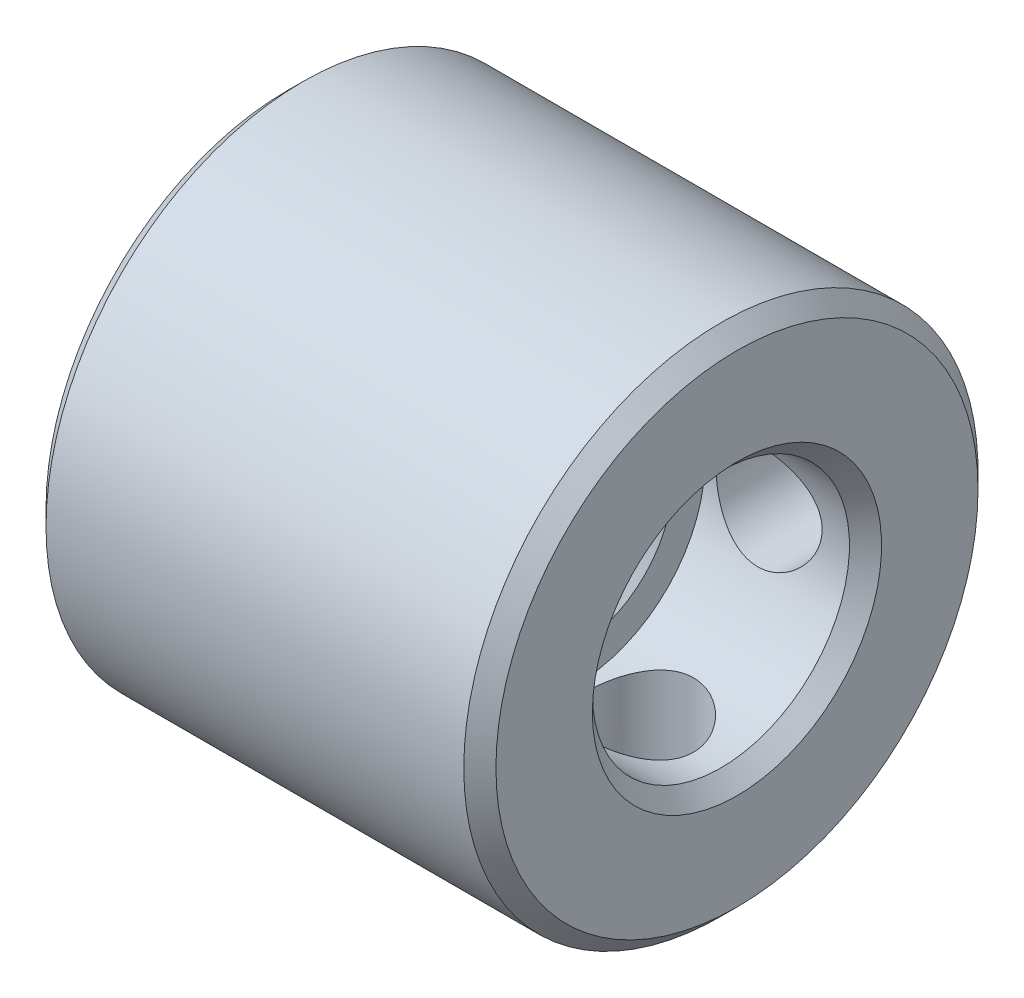
SolidWorks part; units mm, degrees
ref_plane "前视基准面" through (0, 0, 0) normal (0, 0, 1) x (1, 0, 0)
ref_plane "上视基准面" through (0, 0, 0) normal (0, 1, 0) x (1, 0, 0)
ref_plane "右视基准面" through (0, 0, 0) normal (1, 0, 0) x (0, 0, -1)
sketch "草图1" plane through (0, 0, 0) normal (0, 1, 0) x (1, 0, 0)
  line L0 (-5, 0) -> (10.2778, 0)
  line L1 (0, 8.5494) -> (0, -6.358)
  line L2 (0, 2.5) -> (9, 2.5)
  line L3 (9, 2.5) -> (9, 4)
  line L4 (9, 4) -> (14, 4)
  line L5 (14, 4) -> (14, 8)
  line L6 (14, 8) -> (0, 8)
  dimension "D1" = 2.5
  dimension "D2" = 4
  dimension "D3" = 8
  dimension "D4" = 14
  dimension "D5" = 9
  dimension "D6" = 5
revolve "旋转1" add sketch "草图1" angle 360 about L0
chamfer "倒角1" distance 0.5 angle 45 5 edges at (0, 0, 2.5) (9, 0, 2.5) (14, 0, 4) (0, 0, 8) (14, 0, 8)
sketch "草图2" plane through (0, 0, 0) normal (0, 1, 0) x (1, 0, 0)
  line L0 (-3.9253, 0) -> (28.3087, 0) construction
  line L1 (0, 10.279) -> (0, -10.279) construction
  line L2 (14, 7.5) -> (14, -7.5) construction
  line L3 (3, 10.279) -> (3, -10.279) construction
  line L4 (11, 7.5) -> (11, -7.5) construction
  circle A0 centre (3, 0) radius 1.65
  circle A1 centre (11, 0) radius 1.65
  dimension "D3" = 3.3
  dimension "D4" = 3.3
  dimension "D1" = 3
  dimension "D2" = 3
extrude "切除-拉伸1" cut sketch "草图2" against normal blind 10
sketch "草图3" plane through (0, 0, 0) normal (0, 0, 1) x (1, 0, 0)
  line L0 (-2.6359, 0) -> (28.2152, 0) construction
  line L1 (0, 7.5) -> (0, -7.5) construction
  line L2 (0, -7.5) -> (0.5, -8) construction
  line L3 (0, 7.5) -> (0, -7.5) construction
  line L4 (14, 7.5) -> (14, -7.5) construction
  line L5 (3, 7.5) -> (3, -7.5) construction
  line L6 (11, 7.5) -> (11, -7.5) construction
  circle A0 centre (3, 0) radius 1.65
  circle A1 centre (11, 0) radius 1.65
  dimension "D3" = 3.3
  dimension "D4" = 3.3
  dimension "D1" = 3
  dimension "D2" = 3
extrude "切除-拉伸2" cut sketch "草图3" against normal blind 10
